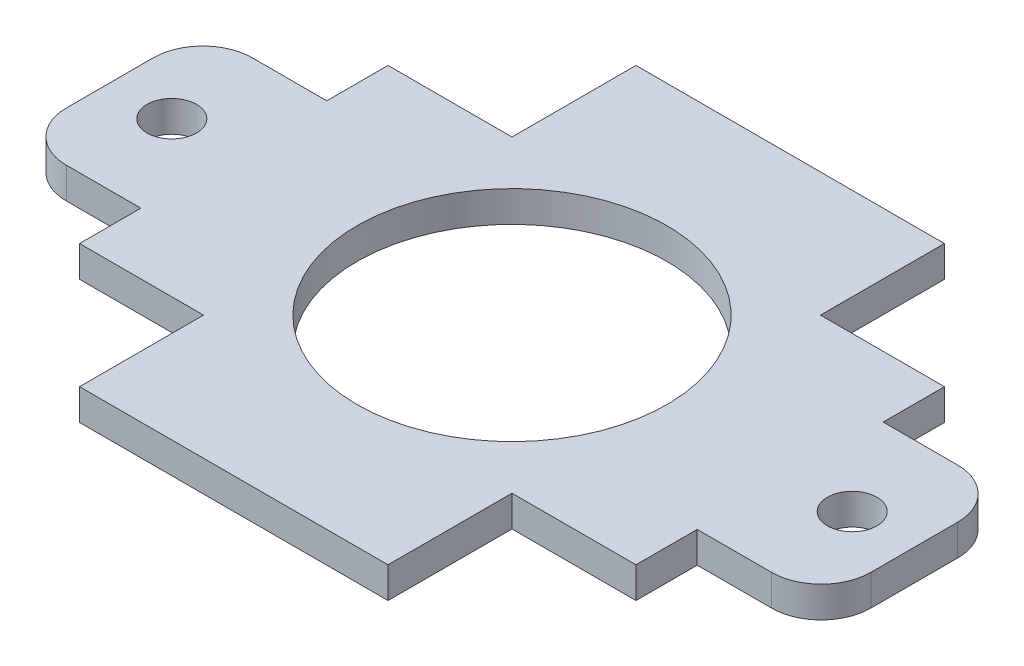
SolidWorks part; units mm, degrees
ref_plane "Front Plane" through (0, 0, 0) normal (0, 0, 1) x (1, 0, 0)
ref_plane "Top Plane" through (0, 0, 0) normal (0, 1, 0) x (1, 0, 0)
ref_plane "Right Plane" through (0, 0, 0) normal (1, 0, 0) x (0, 0, -1)
sketch "Sketch1" plane through (0, 0, 0) normal (0, 1, 0) x (1, 0, 0)
  line L5 (15.8, 15.8) -> (-15.8, -15.8) construction
  line L6 (-28.5, 15.8) -> (-28.5, 9.525)
  line L15 (-28.5, -9.525) -> (-36.12, -9.525)
  line L17 (-28.5, 9.525) -> (-36.12, 9.525)
  line L18 (-41.2, -4.445) -> (-41.2, 4.445)
  line L19 (-15.8, 28.5) -> (15.8, 28.5)
  line L20 (15.8, -28.5) -> (-15.8, -28.5)
  line L22 (15.8, -15.8) -> (-15.8, 15.8) construction
  line L23 (0, -28.5) -> (0, 28.5) construction
  line L24 (28.5, -9.525) -> (36.12, -9.525)
  line L25 (41.2, -4.445) -> (41.2, 4.445)
  line L26 (28.5, 9.525) -> (36.12, 9.525)
  line L29 (-15.8, 15.8) -> (-28.5, 15.8)
  line L30 (-15.8, 15.8) -> (-15.8, 28.5)
  line L35 (15.8, 15.8) -> (28.5, 15.8)
  line L36 (15.8, 15.8) -> (15.8, 28.5)
  line L39 (-28.5, -9.525) -> (-28.5, -15.8)
  line L40 (28.5, 15.8) -> (28.5, 9.525)
  line L41 (15.8, -15.8) -> (28.5, -15.8)
  line L42 (15.8, -15.8) -> (15.8, -28.5)
  line L45 (28.5, -9.525) -> (28.5, -15.8)
  line L47 (-15.8, -15.8) -> (-28.5, -15.8)
  line L48 (-15.8, -15.8) -> (-15.8, -28.5)
  circle A0 centre (0, 0) radius 15.875
  circle A13 centre (-34.85, 0) radius 2.54
  arc A14 (36.12, -9.525) -> (41.2, -4.445) centre (36.12, -4.445) ccw
  arc A15 (41.2, 4.445) -> (36.12, 9.525) centre (36.12, 4.445) ccw
  arc A16 (-36.12, 9.525) -> (-41.2, 4.445) centre (-36.12, 4.445) ccw
  arc A17 (-36.12, -9.525) -> (-41.2, -4.445) centre (-36.12, -4.445) cw
  circle A18 centre (34.85, 0) radius 2.54
  point P9 (-28.5, 0)
  point P38 (0, 0)
  point P55 (41.2, -9.525)
  point P58 (41.2, 9.525)
  dimension "D4" = 12.7
  dimension "D5" = 31.75
  dimension "D6" = 12.7
  dimension "D10" = 6.35
  dimension "D12" = 5.08
  dimension "D13" = 5.08
  dimension "D2" = 12.7
  dimension "D3" = 82.4
  dimension "D7" = 12.7
  dimension "D9" = 19.05
  dimension "D11" = 9.525
  dimension "D8" = 12.7
  dimension "D14" = 12.7
  dimension "D15" = 0
extrude "Boss-Extrude1" add sketch "Sketch1" along normal blind 3.175
